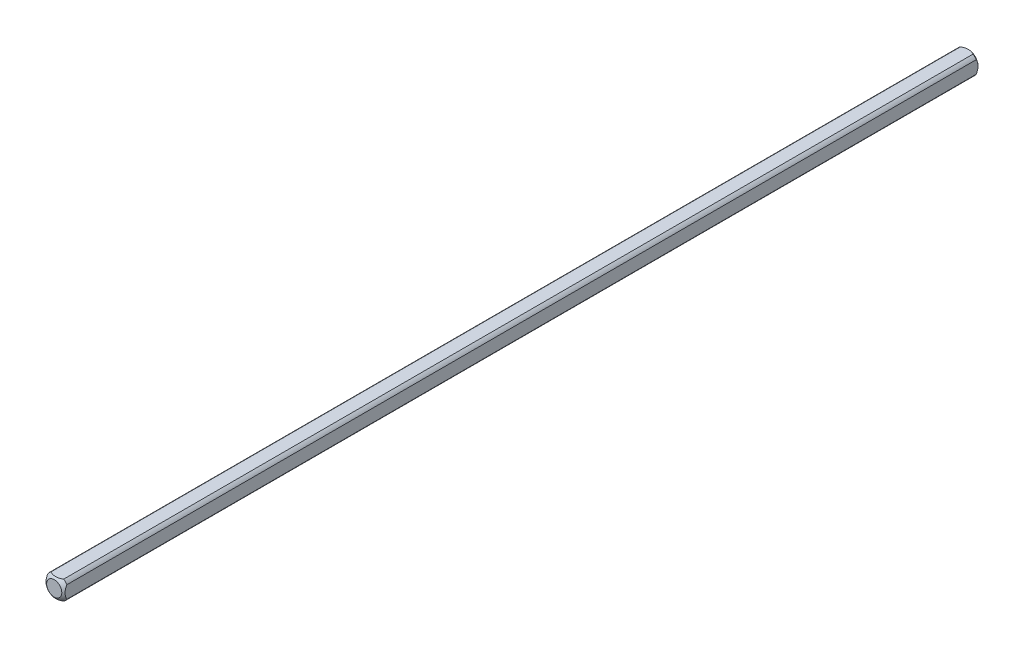
SolidWorks part; units mm, degrees
material "Custom Plastic"
ref_plane "Front Plane" through (0, 0, 0) normal (0, 0, 1) x (1, 0, 0)
ref_plane "Top Plane" through (0, 0, 0) normal (0, 1, 0) x (1, 0, 0)
ref_plane "Right Plane" through (0, 0, 0) normal (1, 0, 0) x (0, 0, -1)
sketch "Sketch1" plane through (0, 0, 0) normal (0, 0, 1) x (1, 0, 0)
  line L0 (-3.175, -3.175) -> (3.175, 3.175) construction
  line L1 (-3.175, -3.175) -> (3.175, -3.175)
  line L2 (-3.175, -3.175) -> (-3.175, 3.175)
  line L3 (-3.175, 3.175) -> (3.175, 3.175)
  line L4 (3.175, -3.175) -> (3.175, 3.175)
  dimension "D1" = 6.35
extrude "Boss-Extrude1" add sketch "Sketch1" along normal blind 152.4
sketch "Sketch2" plane through (0, 0, 0) normal (0, 0, -1) x (-1, 0, 0)
  circle A0 centre (0, 0) radius 3.81
  dimension "D1" = 7.62
extrude "Cut-Extrude1" cut sketch "Sketch2" against normal through all flip side to cut
ref_axis "Axis1" through (0, 0, 152.4) along (0, 0, -1)
sketch "Sketch3" plane through (0, 0, 0) normal (0, 1, 0) x (1, 0, 0)
  line L1 (-5.0537, -3.8933) -> (-5.0537, 5.7405)
  line L2 (-5.0537, 5.7405) -> (0, 5.7405)
  line L5 (0, -152.4) -> (0, 0) construction
  line L8 (0, 0.6703) -> (0, 5.7405)
  arc A0 (-5.0537, -3.8933) -> (0, 0.6703) centre (0, -4.4097) cw
  dimension "D1" = 5.08
revolve "Cut-Revolve1" cut sketch "Sketch3" angle 360 about axis through (0, 0, 152.4) along (0, 0, -1)
mirror "Mirror1" about plane through (0, 0, 152.4) normal (0, 0, -1) of bodies 103
